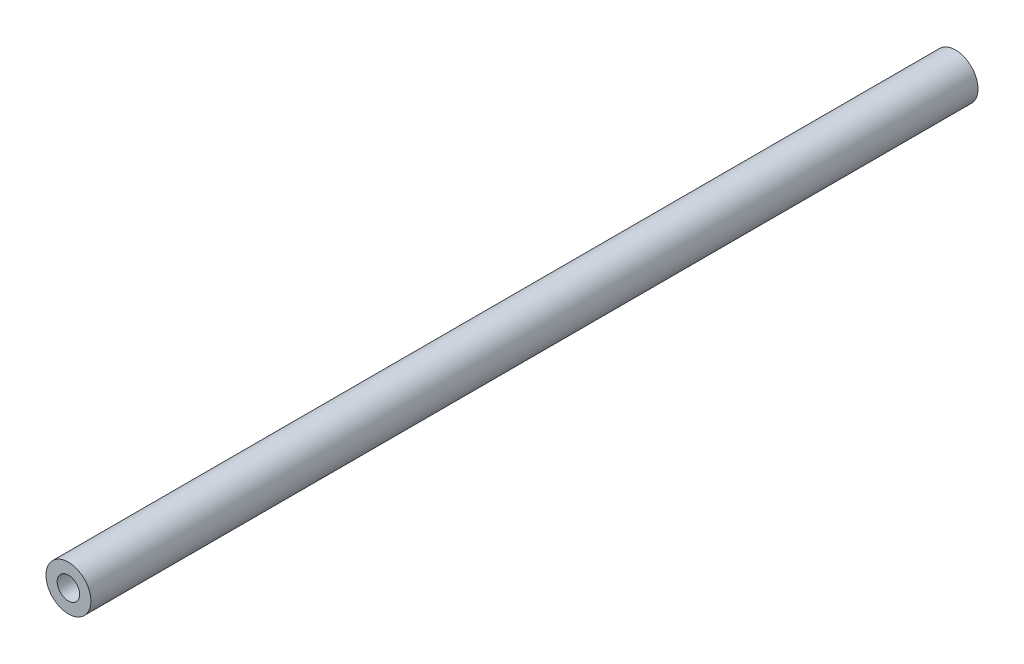
SolidWorks part; units mm, degrees
ref_plane "Front Plane" through (0, 0, 0) normal (0, 0, 1) x (1, 0, 0)
ref_plane "Top Plane" through (0, 0, 0) normal (0, 1, 0) x (1, 0, 0)
ref_plane "Right Plane" through (0, 0, 0) normal (1, 0, 0) x (0, 0, -1)
sketch "Sketch1" plane through (0, 0, 0) normal (0, 0, 1) x (1, 0, 0)
  circle A0 centre (0, 0) radius 1
  circle A1 centre (0, 0) radius 2
  dimension "D1" = 4
  dimension "D2" = 2
extrude "Boss-Extrude1" add sketch "Sketch1" along normal blind 79
